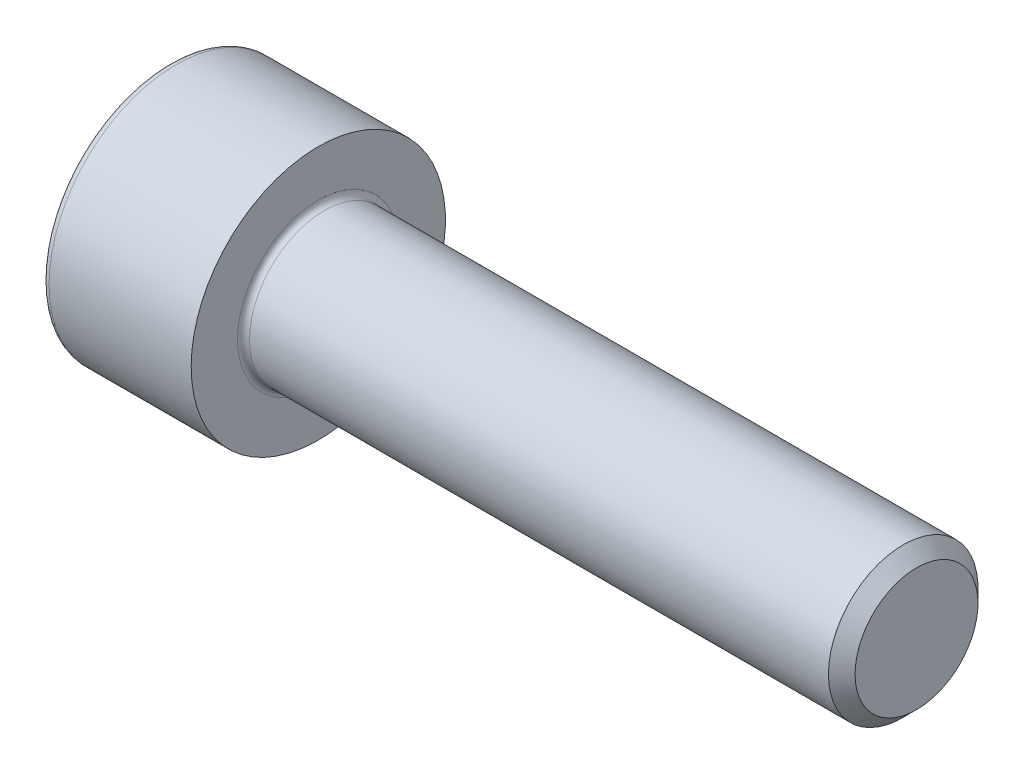
SolidWorks part; units mm, degrees
material "201 Annealed Stainless Steel (SS)"
ref_plane "Plane1" through (0, 0, 0) normal (0, 0, 1) x (1, 0, 0)
ref_plane "Plane2" through (0, 0, 0) normal (0, 1, 0) x (1, 0, 0)
ref_plane "Plane3" through (0, 0, 0) normal (1, 0, 0) x (0, 0, -1)
sketch "BodySke" plane through (0, 0, 0) normal (0, 0, 1) x (1, 0, 0)
  line L0 (0, 0) -> (0, 4.25)
  line L1 (0, 4.25) -> (5, 4.25)
  line L2 (5, 4.25) -> (5, 2.5)
  line L3 (5, 2.5) -> (24.555, 2.5)
  line L4 (25, 2.055) -> (25, 0)
  line L5 (25, 0) -> (0, 0)
  line L6 (-31.75, 0) -> (127, 0) construction
  line L8 (25, 2.055) -> (24.555, 2.5)
  line L10 (25, -2.055) -> (24.555, -2.5) construction
  line L11 (5.8, 9.525) -> (5.8, 3.175) construction
  line L12 (5, 9.525) -> (5, 3.175) construction
  line L13 (-35, 9.525) -> (-35, 3.175) construction
  dimension "Diameter" = 5
  dimension "Head_ht" = 5
  dimension "Length" = 20
  dimension "Body_ch_ang" = 45
  dimension "Head_dia" = 8.5
  dimension "Minor_dia" = 4.11
  dimension "Advance" = 0.8
  dimension "Thread_nom" = 20
  dimension "Thread_length" = 60
revolve "Base-Revolve" add sketch "BodySke"
cosmetic thread "ThreadCosmetic" [suppressed]
fillet "Fillet1" radius 0.2 1 edges at (5, 0, 2.5)
fillet "Fillet2" radius 0.25 1 edges at (0, 0, 4.25)
sketch "Sketch2" plane through (0, 0, 0) normal (0, 0, 1) x (1, 0, 0)
  line L0 (0, 2.042) -> (2.5, 2.042)
  line L1 (2.5, 2.042) -> (3.6789, 0)
  line L2 (-31.75, 0) -> (127, 0) construction
  line L3 (3.6789, 0) -> (0, 0)
  line L4 (0, 0) -> (0, 2.042)
  line L6 (0, 0) -> (47.625, 0) construction
  dimension "D1" = 2.042
  dimension "D2" = 60
  dimension "Depth" = 2.5
revolve "Hex-PreBroach" cut sketch "Sketch2" angle 360 about L6
sketch "Sketch3" plane through (0, 0, 0) normal (-1, 0, 0) x (0, 0.5, 0.866)
  line L0 (1.1789, 2.042) -> (-1.1789, 2.042)
  line L1 (-1.1789, 2.042) -> (-2.3579, 0)
  line L2 (1.1789, 2.042) -> (2.3579, 0)
  line L3 (1.1789, -2.042) -> (2.3579, 0)
  line L4 (1.1789, -2.042) -> (-1.1789, -2.042)
  line L5 (-1.1789, -2.042) -> (-2.3579, 0)
  dimension "D1" = 2.042
  dimension "D2" = 2.042
  dimension "Hex_size" = 4.084
extrude "Hex" cut sketch "Sketch3" against normal blind 2.5
sketch "ThdSchSke" plane through (0, 0, 0) normal (0, 0, 1) x (1, 0, 0)
  line L0 (7.4, -2.055) -> (7.0884, -2.5)
  line L1 (7.4, -2.055) -> (7.7116, -2.5)
  line L2 (7.7116, -2.5) -> (7.7116, -3.125)
  line L3 (-3.175, 0) -> (5.1513, 0) construction
  line L4 (0, 4) -> (0, -4) construction
  line L5 (7.7116, -3.125) -> (7.0884, -3.125)
  line L6 (7.0884, -3.125) -> (7.0884, -2.5)
  dimension "Thread_minor" = 4.11
  dimension "Diameter" = 5
  dimension "Start" = 7.4
  dimension "SideAngle" = 55
  dimension "VeeAngle" = 70
  dimension "Overcut" = 6.25
revolve "ThreadSchematic" [suppressed] cut sketch "ThdSchSke" angle 360 about L3
pattern_linear "ThdSchPat" [suppressed]
equation "\"D2@Sketch3\" = \"Hex_size@Sketch3\" / 2"
equation "\"D1@Sketch3\" = \"Hex_size@Sketch3\" / 2"
equation "\"D1@Sketch2\" = \"Hex_size@Sketch3\" / 2"
equation "\"Thread_minor@ThreadCosmetic\"  =  \"Minor_dia@BodySke\""
equation "\"Depth@Sketch2\" =  \"Key_eng@Hex\""
equation "\"Thread_length@ThreadCosmetic\" = ((sgn( (\"Length@BodySke\" - \"Advance@BodySke\" * 3.0) - \"Thread_nom@BodySke\" )-1)*( (\"Length@BodySke\" - \"Advance@BodySke\" * 3.0) - \"Thread_nom@BodySke\" ))/-2+ \"Thread_nom@BodySke\""
equation "\"Thread_minor@ThdSchSke\" = \"Minor_dia@BodySke\""
equation "\"Diameter@ThdSchSke\" = \"Diameter@BodySke\""
equation "\"Overcut@ThdSchSke\" = \"Diameter@BodySke\" * 1.25"
equation "\"Start@ThdSchSke\" = \"Head_ht@BodySke\" + \"Length@BodySke\" - \"Thread_length@ThreadCosmetic\"  '---Non-countersunk---"
equation "\"Num_threads@ThdSchPat\" = int( \"Thread_length@ThreadCosmetic\" / \"Advance@BodySke\" + 0.999 )  + 1"
equation "\"Advance@ThdSchPat\" = \"Thread_length@ThreadCosmetic\" /  (\"Num_threads@ThdSchPat\" - 1) 'relax it"
equation "\"Num_threads@ThdSchPat\" = \"Num_threads@ThdSchPat\" - sgn( \"Num_threads@ThdSchPat\" - 1) '---chamfered tips only---"
